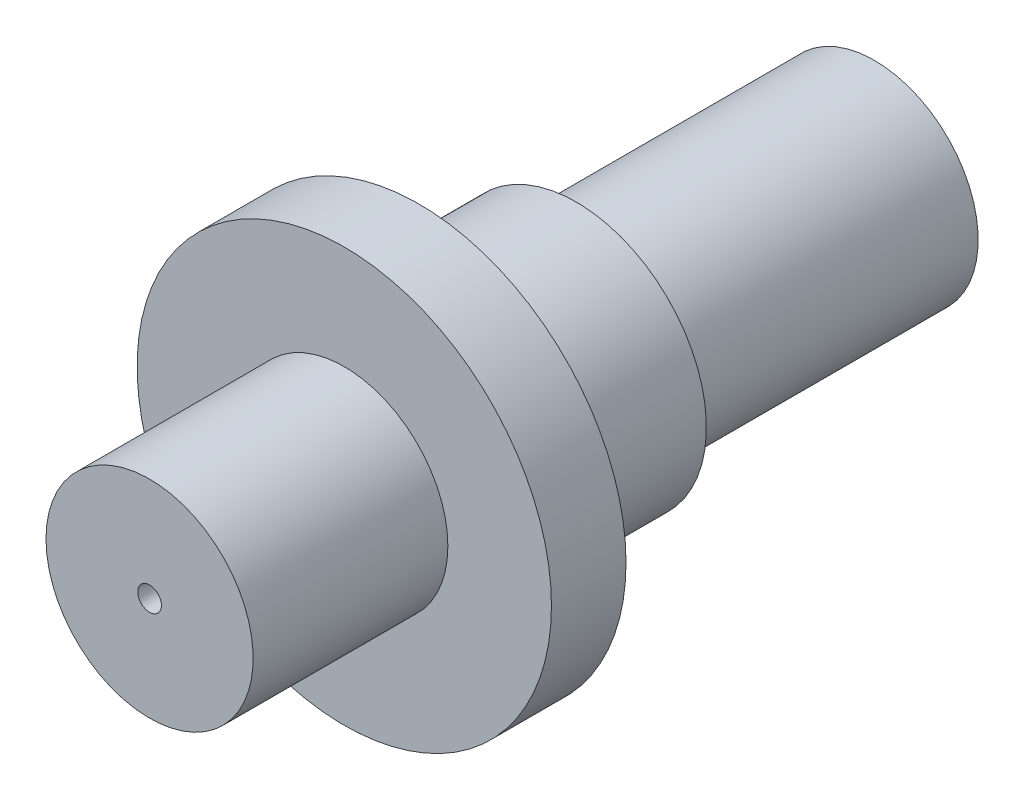
SolidWorks part; units mm, degrees
ref_plane "Front Plane" through (0, 0, 0) normal (0, 0, 1) x (1, 0, 0)
ref_plane "Top Plane" through (0, 0, 0) normal (0, 1, 0) x (1, 0, 0)
ref_plane "Right Plane" through (0, 0, 0) normal (1, 0, 0) x (0, 0, -1)
sketch "Sketch1" plane through (0, 0, 0) normal (0, 0, 1) x (1, 0, 0)
  circle A0 centre (0, 0) radius 6.35
  dimension "D1" = 12.7
extrude "Boss-Extrude1" add sketch "Sketch1" along normal blind 2.286
sketch "Sketch2" plane through (0, 0, 0) normal (0, 0, -1) x (-1, 0, 0)
  circle A0 centre (0, 0) radius 3.175
  dimension "D1" = 6.35
extrude "Boss-Extrude2" add sketch "Sketch2" against normal blind 8.255
sketch "Sketch3" plane through (0, 0, 0) normal (0, 0, -1) x (-1, 0, 0)
  circle A0 centre (0, 0) radius 3.9878
  dimension "D1" = 7.9756
extrude "Boss-Extrude3" add sketch "Sketch3" along normal blind 4.826
sketch "Sketch4" plane through (0, 0, -4.826) normal (0, 0, -1) x (-1, 0, 0)
  circle A0 centre (0, 0) radius 3.175
  dimension "D1" = 6.35
extrude "Boss-Extrude4" add sketch "Sketch4" along normal offset from surface (9.144 mm away) 22.225 up to face at (-3.175, 0, 8.255)
sketch "Sketch5" plane through (0, 0, 8.255) normal (0, 0, 1) x (1, 0, 0)
  circle A0 centre (0, 0) radius 0.3629
extrude "Cut-Extrude1" cut sketch "Sketch5" against normal through all
